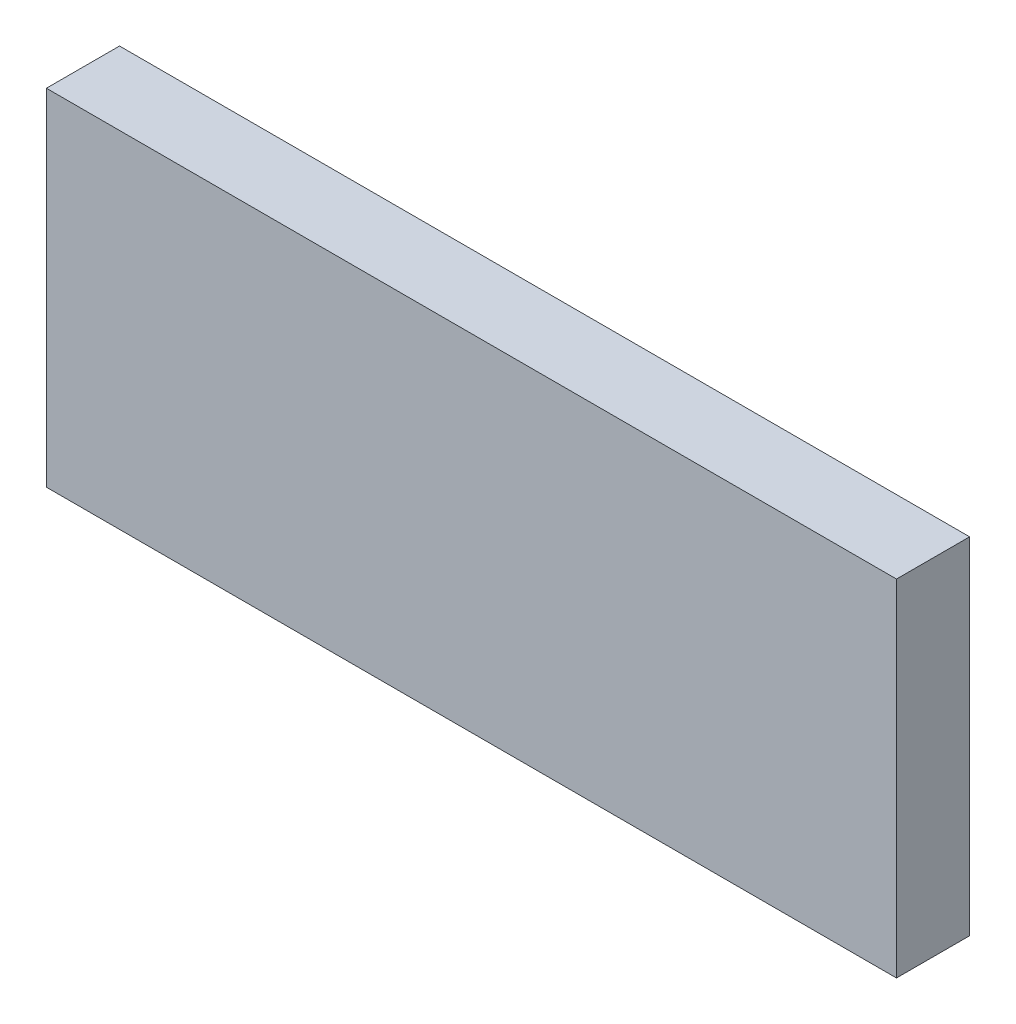
SolidWorks part; units mm, degrees
ref_plane "Plan de face" through (0, 0, 0) normal (0, 0, 1) x (1, 0, 0)
ref_plane "Plan de dessus" through (0, 0, 0) normal (0, 1, 0) x (1, 0, 0)
ref_plane "Plan de droite" through (0, 0, 0) normal (1, 0, 0) x (0, 0, -1)
sketch "Esquisse1" plane through (0, 0, 0) normal (0, 0, 1) x (1, 0, 0)
  line L1 (0, 0) -> (-93, 0)
  line L2 (0, 0) -> (0, 37.8)
  line L3 (0, 37.8) -> (-93, 37.8)
  line L4 (-93, 0) -> (-93, 37.8)
  dimension "D1" = 93
  dimension "D2" = 37.8
extrude "Boss.-Extru.1" add sketch "Esquisse1" along normal blind 8
